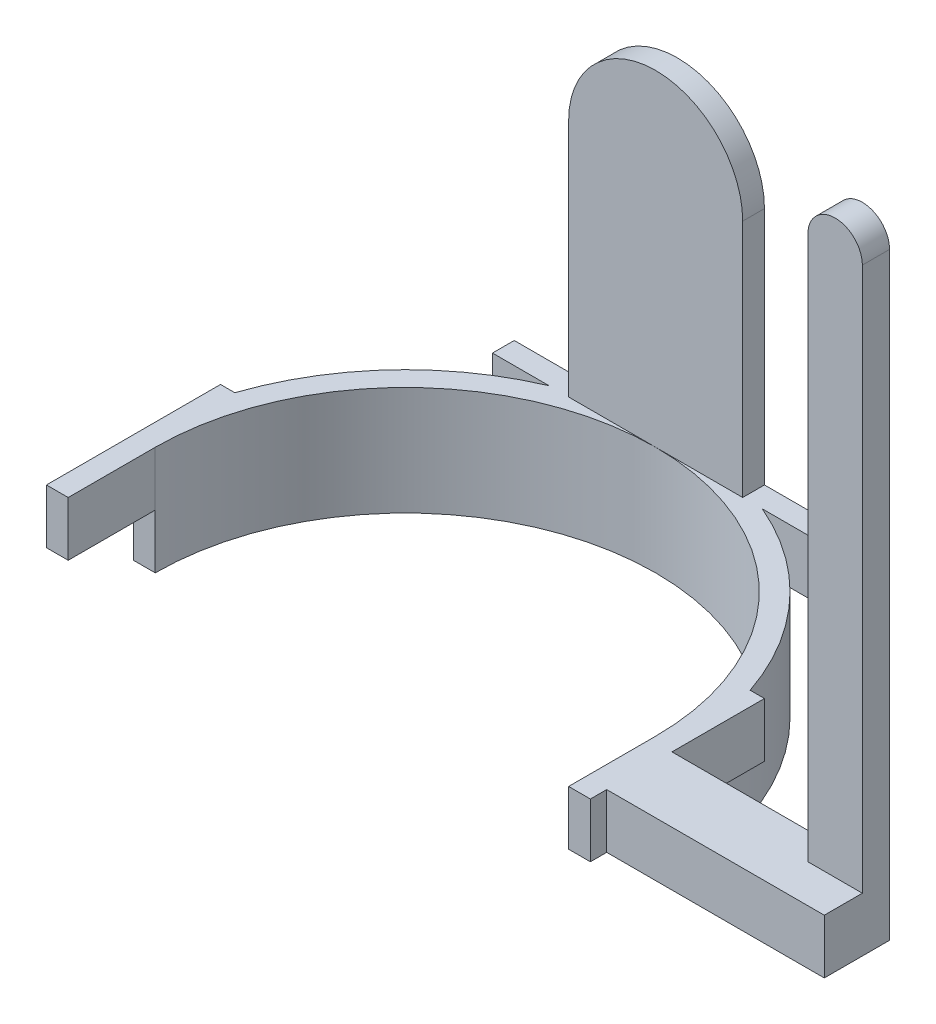
SolidWorks part; units mm, degrees
ref_plane "Front" through (0, 0, 0) normal (0, 0, 1) x (1, 0, 0)
ref_plane "Top" through (0, 0, 0) normal (0, 1, 0) x (1, 0, 0)
ref_plane "Right" through (0, 0, 0) normal (1, 0, 0) x (0, 0, -1)
sketch "草图1" plane through (0, 0, 0) normal (0, 1, 0) x (1, 0, 0)
  line L0 (-39.7033, 0) -> (64.2421, 0) construction
  line L1 (-50, 0) -> (-46, 0)
  line L2 (46, 0) -> (50, 0)
  arc A0 (-50, 0) -> (50, 0) centre (0, 0) cw
  arc A1 (-46, 0) -> (46, 0) centre (0, 0) cw
extrude "凸台-拉伸1" add sketch "草图1" along normal blind 10
sketch "草图3" plane through (0, 10, 0) normal (0, 1, 0) x (1, 0, 0)
  line L0 (46, 0) -> (50, 0) construction
  line L1 (-50, 0) -> (-46, 0) construction
  line L2 (-50, 16) -> (-47.3709, 16)
  line L3 (-50, 16) -> (-50, -16)
  line L4 (-50, -16) -> (-46, -16)
  line L5 (-46, 0) -> (-46, -16)
  line L6 (50, 16) -> (47.3709, 16)
  line L7 (50, 16) -> (50, -16)
  line L8 (50, -16) -> (46, -16)
  line L9 (46, 0) -> (46, -16)
  line L10 (0, 0) -> (0, 56.0177) construction
  line L11 (-26.9117, 46) -> (-19.5959, 46) construction
  line L12 (-22.8935, 50) -> (37.5767, 50) construction
  line L13 (19.5959, 46) -> (38.2628, 46) construction
  line L14 (-30, 50) -> (30, 50)
  line L15 (-30, 50) -> (-30, 46)
  line L16 (-30, 46) -> (-19.5959, 46)
  line L17 (30, 50) -> (30, 46)
  line L18 (19.5959, 46) -> (30, 46)
  arc A0 (-47.3709, 16) -> (-19.5959, 46) centre (0, 0) cw
  arc A1 (-46, 0) -> (46, 0) centre (0, 0) cw
  arc A2 (19.5959, 46) -> (47.3709, 16) centre (0, 0) cw
  dimension "D1" = 32
  dimension "D2" = 16
  dimension "D3" = 32
  dimension "D4" = 16
  dimension "D5" = 60
  dimension "D6" = 30
extrude "凸台-拉伸2" add sketch "草图3" along normal blind 10
sketch "草图4" plane through (0, 20, 0) normal (0, 1, 0) x (1, 0, 0)
  line L5 (0, 50) -> (0, 35.5033) construction
  line L6 (30, 50) -> (-30, 50) construction
  line L8 (-16, 50) -> (16, 50)
  line L9 (-16, 50) -> (-16, 46)
  line L10 (-16, 46) -> (16, 46)
  line L11 (16, 50) -> (16, 46)
  dimension "D1" = 16
  dimension "D2" = 16
extrude "凸台-拉伸3" add sketch "草图4" along normal blind 60
sketch "草图5" plane through (0, 0, -50) normal (0, 0, -1) x (-1, 0, 0)
  line L2 (-16, 64) -> (-16, 97.9053)
  line L3 (-16, 97.9053) -> (16, 97.9053)
  line L4 (16, 64) -> (16, 97.9053)
  arc A0 (16, 64) -> (-16, 64) centre (0, 64) ccw
extrude "切除-拉伸1" cut sketch "草图5" against normal blind 30
sketch "草图6" plane through (50, 0, 0) normal (1, 0, 0) x (0, 0, -1)
  line L0 (-16, 20) -> (16, 20) construction
  line L1 (-13, 20) -> (-1, 20)
  line L2 (-13, 20) -> (-13, 10)
  line L3 (-13, 10) -> (-1, 10)
  line L4 (-1, 20) -> (-1, 10)
  line L5 (-16, 10) -> (0, 10) construction
  line L6 (0, 10) -> (0, 0) construction
  dimension "D1" = 13
  dimension "D2" = 12
extrude "凸台-拉伸4" add sketch "草图6" along normal blind 40
sketch "草图7" plane through (0, 20, 0) normal (0, 1, 0) x (1, 0, 0)
  line L1 (90, -1) -> (80, -1)
  line L2 (90, -1) -> (90, -6)
  line L3 (90, -6) -> (80, -6)
  line L4 (80, -1) -> (80, -6)
  dimension "D1" = 5
  dimension "D2" = 10
extrude "凸台-拉伸5" add sketch "草图7" along normal blind 100
sketch "草图8" plane through (0, 0, 1) normal (0, 0, -1) x (-1, 0, 0)
  line L0 (-90, 120) -> (-80, 120) construction
  circle A0 centre (-85, 120) radius 5
extrude "凸台-拉伸6" add sketch "草图8" against normal blind 5
